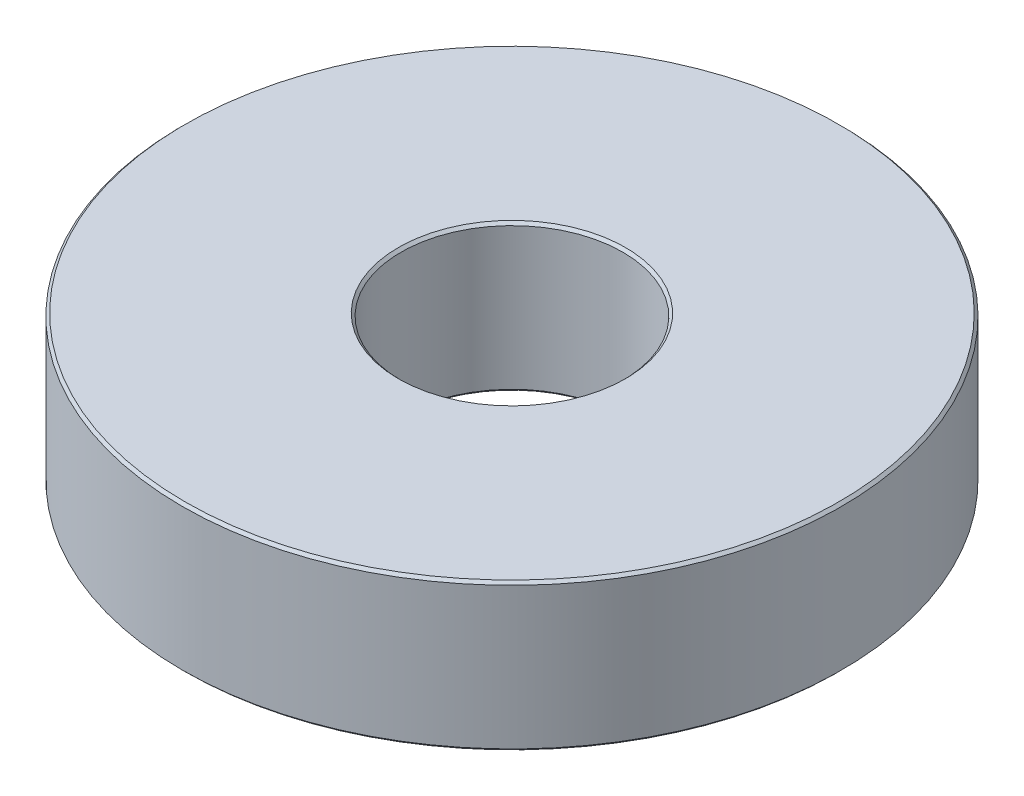
SolidWorks part; units mm, degrees
ref_plane "Front Plane" through (0, 0, 0) normal (0, 0, 1) x (1, 0, 0)
ref_plane "Top Plane" through (0, 0, 0) normal (0, 1, 0) x (1, 0, 0)
ref_plane "Right Plane" through (0, 0, 0) normal (1, 0, 0) x (0, 0, -1)
sketch "Sketch1" plane through (0, 0, 0) normal (0, 1, 0) x (1, 0, 0)
  circle A0 centre (0, 0) radius 12.325
  circle A1 centre (0, 0) radius 4.15
  dimension "D1" = 24.65
  dimension "D2" = 8.3
extrude "Boss-Extrude1" add sketch "Sketch1" along normal blind 5.5
chamfer "Chamfer1" distance 0.1 angle 45 4 edges at (0, 0, 4.15) (0, 0, 12.325) (0, 5.5, 4.15) (0, 5.5, 12.325)
